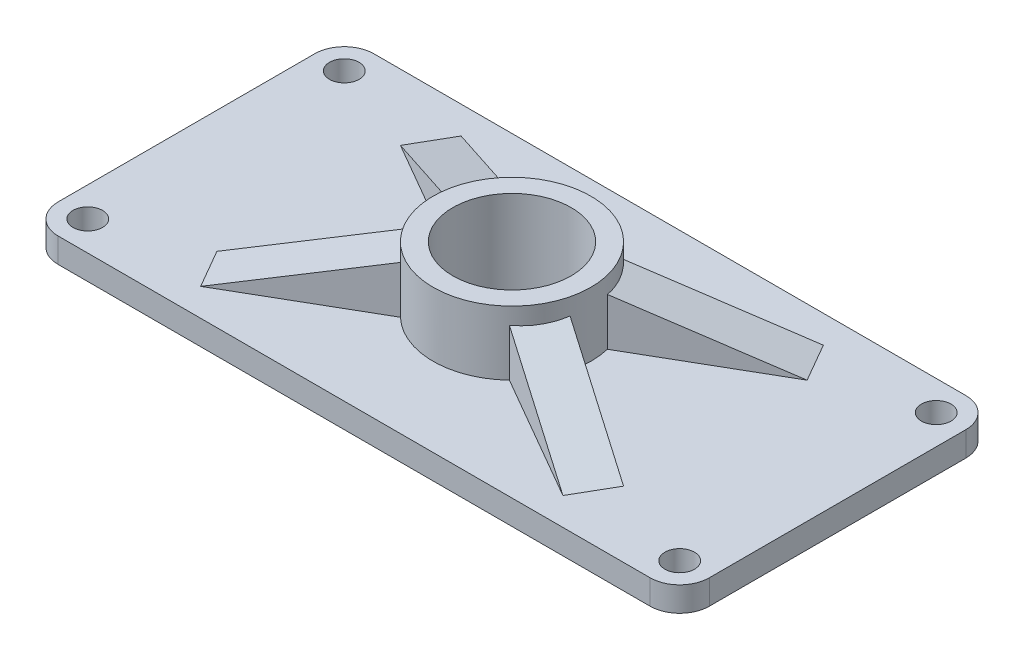
SolidWorks part; units mm, degrees
ref_plane "Front Plane" through (0, 0, 0) normal (0, 0, 1) x (1, 0, 0)
ref_plane "Top Plane" through (0, 0, 0) normal (0, 1, 0) x (1, 0, 0)
ref_plane "Right Plane" through (0, 0, 0) normal (1, 0, 0) x (0, 0, -1)
sketch "Sketch1" plane through (0, 0, 0) normal (0, 1, 0) x (1, 0, 0)
  line L1 (-60, -32) -> (60, -32)
  line L2 (-66, -26) -> (-66, 26)
  line L3 (-60, 32) -> (60, 32)
  line L4 (66, -26) -> (66, 26)
  line L5 (-66, -32) -> (66, 32) construction
  line L6 (-66, 32) -> (66, -32) construction
  arc A0 (-60, -32) -> (-66, -26) centre (-60, -26) cw
  arc A1 (60, -32) -> (66, -26) centre (60, -26) ccw
  arc A2 (60, 32) -> (66, 26) centre (60, 26) cw
  arc A3 (-66, 26) -> (-60, 32) centre (-60, 26) cw
  circle A4 centre (-60, 26) radius 3
  circle A5 centre (60, 26) radius 3
  circle A6 centre (60, -26) radius 3
  circle A7 centre (-60, -26) radius 3
  circle A8 centre (0, 0) radius 12
  point P0 (0, 0)
  dimension "D3" = 6
  dimension "D4" = 6
  dimension "D7" = 24
  dimension "D1" = 132
  dimension "D2" = 64
  dimension "D5" = 2
  dimension "D6" = 2
extrude "Boss-Extrude1" add sketch "Sketch1" along normal blind 5
sketch "Sketch2" plane through (0, 5, 0) normal (0, 1, 0) x (1, 0, 0)
  circle A0 centre (0, 0) radius 12
  circle A1 centre (0, 0) radius 16
  point P4 (0, 0)
  dimension "D1" = 32
  dimension "D2" = 24
extrude "Boss-Extrude2" add sketch "Sketch2" along normal blind 13
sketch "Sketch3" plane through (0, 5, 0) normal (0, 1, 0) x (1, 0, 0)
  line L0 (0, 0) -> (-61.4923, -35.5026) construction
  line L1 (-61.4923, -35.5026) -> (61.4923, 35.5026) construction
  line L2 (0, 0) -> (-66, 0) construction
  line L3 (-66, 26) -> (-66, -26) construction
  dimension "D1" = 30
ref_plane "Plane1" through (0, 0, 0) normal (-0.5, 0, -0.866) x (-0.866, 0, 0.5)
sketch "Sketch5" plane through (0, 0, 0) normal (-0.5, 0, -0.866) x (-0.866, 0, 0.5)
  line L0 (-45, 5) -> (-16, 14.4227)
  line L1 (71.0052, 5) -> (-71.0052, 5) construction
  line L2 (-16, 18) -> (-16, 5) construction
  dimension "D1" = 45
  dimension "D2" = 162
rib "Rib1" sketch "Sketch5" sketch "Sketch5" thickness 9 extrusion direction parallel to sketch draft on no parameters "D1"=9
pattern_circular "CirPattern1" count 2 over 360 of "Rib1"
mirror "Mirror1" about plane through (0, 0, 0) normal (1, 0, 0) of "CirPattern1", "Rib1"
